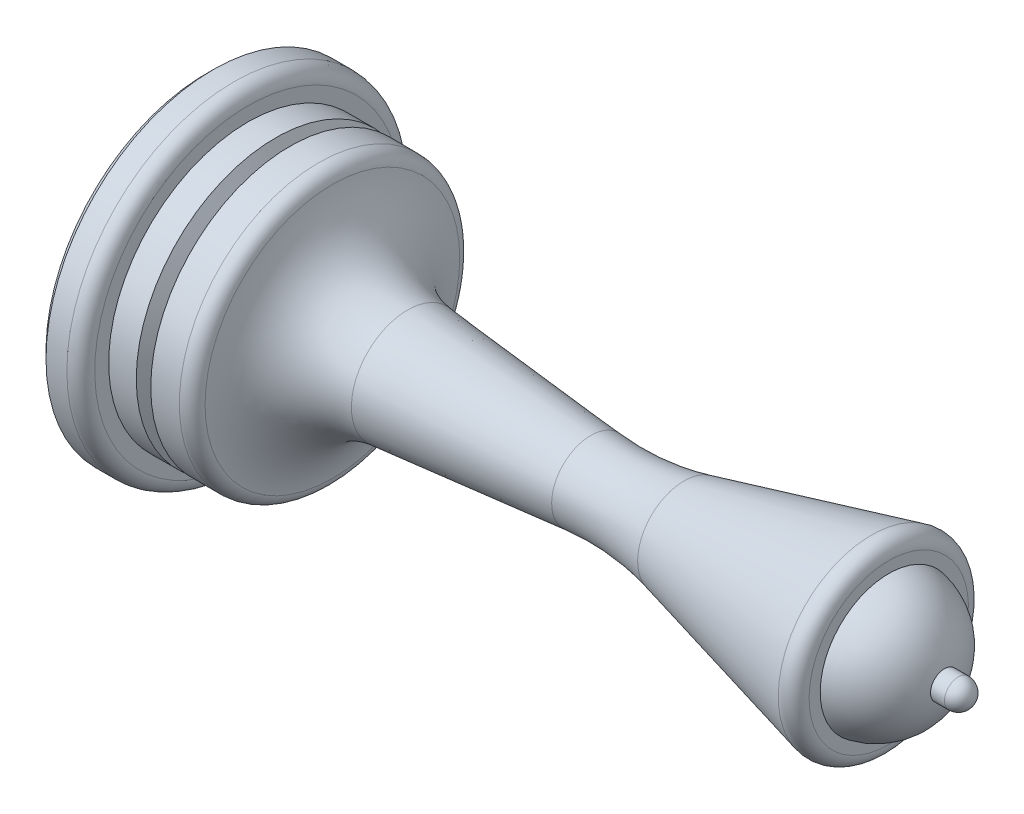
SolidWorks part; units mm, degrees
ref_plane "Front Plane" through (0, 0, 0) normal (0, 0, 1) x (1, 0, 0)
ref_plane "Top Plane" through (0, 0, 0) normal (0, 1, 0) x (1, 0, 0)
ref_plane "Right Plane" through (0, 0, 0) normal (1, 0, 0) x (0, 0, -1)
sketch "Sketch1" plane through (0, 0, 0) normal (0, 0, 1) x (1, 0, 0)
  line L0 (0, 0) -> (0, 11.5)
  line L1 (0.5, 12) -> (2, 12)
  line L2 (3, 11) -> (3, 10)
  line L3 (3, 10) -> (8.0718, 10)
  line L4 (14.4494, 4.0253) -> (27.6133, 2.8121)
  line L5 (54, 1) -> (53, 1)
  line L6 (49, 7) -> (49, 4.9185)
  line L7 (0, 0) -> (55, 0)
  line L8 (0, 0) -> (-16.2845, 0) construction
  line L9 (55, 0) -> (55, -26.6806) construction
  line L10 (49, 7) -> (34.2995, 3.3249)
  line L13 (28.2223, 27.0457) -> (53.7777, 27.0457) construction
  line L14 (0, 11.5) -> (0.5, 12)
  arc A0 (9.0615, 9.1429) -> (14.4494, 4.0253) centre (15, 10) ccw
  arc A1 (27.6133, 2.8121) -> (34.2995, 3.3249) centre (29.4488, 22.7277) ccw
  arc A2 (2, 12) -> (3, 11) centre (2, 11) cw
  arc A3 (8.0718, 10) -> (9.0615, 9.1429) centre (8.0718, 9) cw
  arc A4 (49, 4.9185) -> (53, 1) centre (48.101, 0) cw
  arc A5 (55, 0) -> (54, 1) centre (54, 0) ccw
  point P1 (0, 12)
  point P20 (3, 12)
  point P23 (9, 10)
  point P24 (31, 2.5)
  dimension "D8" = 24
  dimension "D13" = 6
  dimension "D14" = 1
  dimension "D15" = 1
  dimension "D9" = 20
  dimension "D11" = 5
  dimension "D2" = 24
  dimension "D3" = 3
  dimension "D4" = 20
  dimension "D5" = 6
  dimension "D6" = 5
  dimension "D7" = 55
  dimension "D10" = 7
  dimension "D12" = 6
  dimension "D16" = 2
revolve "Revolve1" add sketch "Sketch1" angle 360 about L7
sketch "Sketch2" plane through (0, 0, 0) normal (0, 0, 1) x (1, 0, 0)
  line L0 (4.9794, 10) -> (5.5, 9)
  line L1 (8.0718, 10) -> (3, 10) construction
  line L2 (5.5, 9) -> (6.0206, 10)
  line L3 (4.9794, 10) -> (6.0206, 10)
  line L4 (5.5, 9) -> (5.5, 10) construction
  line L5 (3, -10) -> (3, 10) construction
  line L6 (0, 0) -> (11.1779, 0) construction
  dimension "D1" = 55
  dimension "D2" = 1
  dimension "D3" = 2.5
revolve "Cut-Revolve1" cut sketch "Sketch2" angle 360 about L6
sketch "Sketch3" plane through (0, 0, 0) normal (-1, 0, 0) x (0, 0, 1)
  circle A0 centre (0, 0) radius 6
  dimension "D1" = 12
extrude "Cut-Extrude1" cut sketch "Sketch3" against normal blind 5
fillet "Fillet1" radius 1 1 edges at (49, -7, 0)
